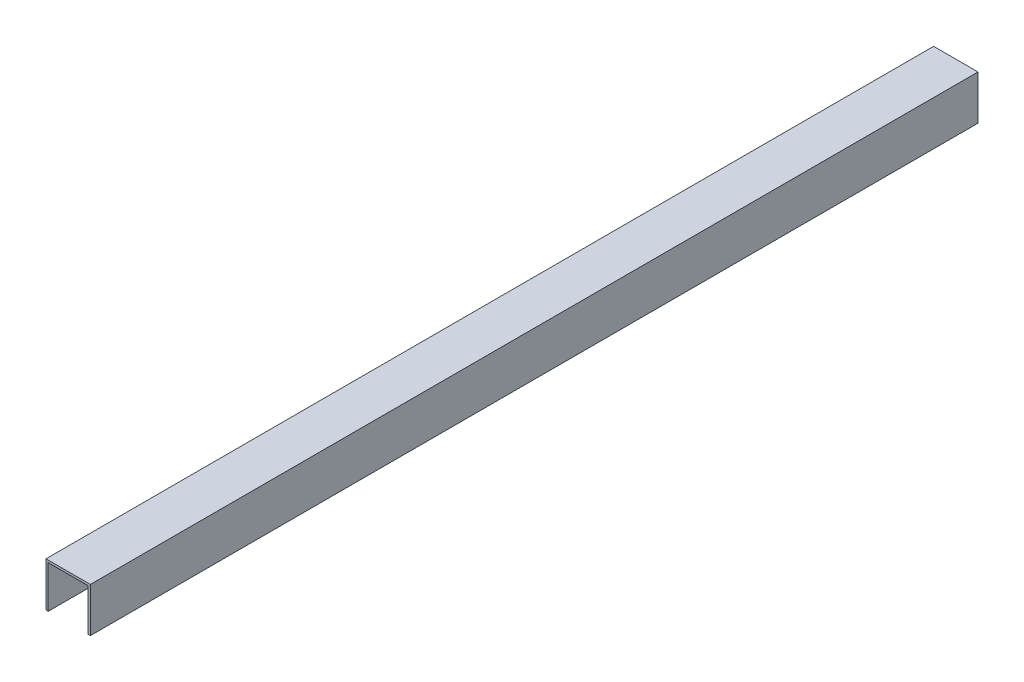
SolidWorks part; units mm, degrees
ref_plane "Plan de face" through (0, 0, 0) normal (0, 0, 1) x (1, 0, 0)
ref_plane "Plan de dessus" through (0, 0, 0) normal (0, 1, 0) x (1, 0, 0)
ref_plane "Plan de droite" through (0, 0, 0) normal (1, 0, 0) x (0, 0, -1)
sketch "Esquisse2" plane through (0, 0, 0) normal (0, 0, 1) x (1, 0, 0)
  line L0 (-107.4415, -9.2332) -> (-107.4415, 0.7668)
  line L1 (-107.4415, 0.7668) -> (-97.4415, 0.7668)
  line L2 (-97.4415, 0.7668) -> (-97.4415, -9.2332)
  line L3 (-97.4415, -9.2332) -> (-97.9415, -9.2332)
  line L4 (-97.9415, -9.2332) -> (-97.9415, 0.2668)
  line L5 (-97.9415, 0.2668) -> (-106.9415, 0.2668)
  line L6 (-106.9415, 0.2668) -> (-106.9415, -9.2332)
  line L7 (-106.9415, -9.2332) -> (-107.4415, -9.2332)
  dimension "D1" = 0.5
  dimension "D2" = 0.5
  dimension "D3" = 0.5
  dimension "D4" = 10
  dimension "D5" = 10
  dimension "D6" = 9
extrude "Boss.-Extru.1" add sketch "Esquisse2" along normal blind 200
